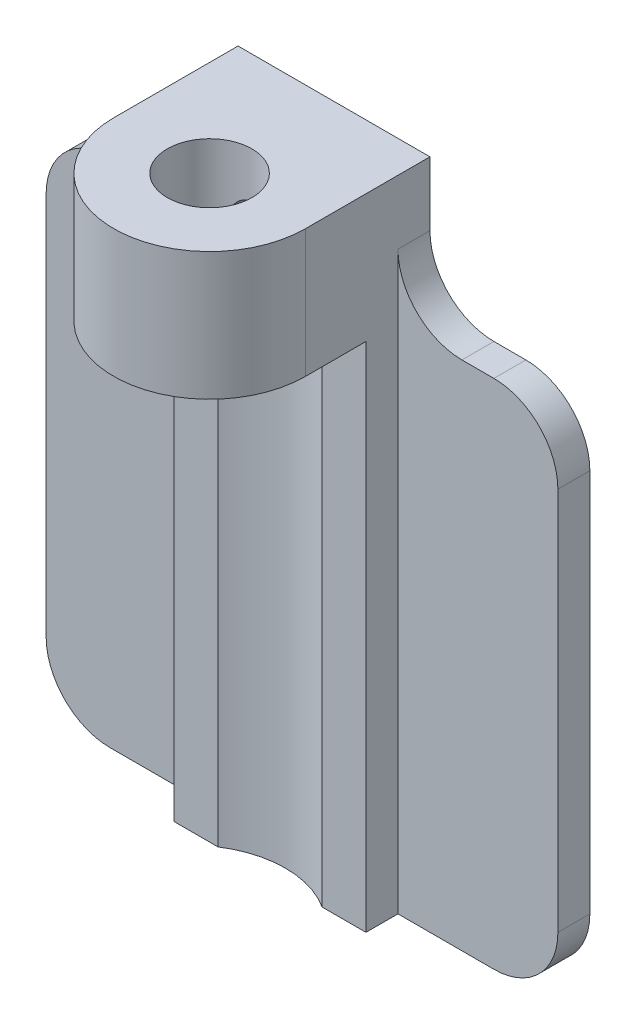
SolidWorks part; units mm, degrees
material "6061-T6 (SS)"
ref_plane "Front Plane" through (0, 0, 0) normal (0, 0, 1) x (1, 0, 0)
ref_plane "Top Plane" through (0, 0, 0) normal (0, 1, 0) x (1, 0, 0)
ref_plane "Right Plane" through (0, 0, 0) normal (1, 0, 0) x (0, 0, -1)
sketch "Sketch2" plane through (0, 0, 0) normal (1, 0, 0) x (0, 0, -1)
  line L0 (-4.7625, 12.7) -> (3, 12.7)
  line L1 (3, 12.7) -> (3, -12.7)
  line L2 (3, -12.7) -> (6.175, -12.7)
  line L3 (6.175, -12.7) -> (6.175, 19.05)
  line L4 (6.175, 19.05) -> (-4.7625, 19.05)
  line L5 (-4.7625, 19.05) -> (-4.7625, 12.7)
  line L6 (0, -1000) -> (0, 49000) construction
  dimension "D1" = 3
  dimension "D2" = 25.4
  dimension "D3" = 3.175
  dimension "D4" = 6.35
  dimension "D5" = 4.7625
  dimension "D6" = 12.7
extrude "Boss-Extrude1" add sketch "Sketch2" along normal mid plane 9.525
sketch "Sketch3" plane through (0, 19.05, 0) normal (0, 1, 0) x (1, 0, 0)
  circle A0 centre (0, 0) radius 2.1
  dimension "D1" = 4.2
extrude "Cut-Extrude1" cut sketch "Sketch3" against normal through all
sketch "Sketch4" plane through (0, -12.7, 0) normal (0, -1, 0) x (1, 0, 0)
  line L0 (4.7625, -3) -> (-4.7625, -3) construction
  circle A0 centre (0, 1.0005) radius 4.7625
  dimension "D1" = 9.525
  dimension "D2" = 0.762
extrude "Cut-Extrude2" cut sketch "Sketch4" against normal up to surface (25.4 mm away) up to face at (0, 12.7, 2.1)
ref_plane "Plane1" through (0, 0, -3.508) normal (0, 0, 1) x (1, 0, 0)
sketch "Sketch5" plane through (0, 0, -6.175) normal (0, 0, -1) x (-1, 0, 0)
  line L0 (2.5841, -12.7) -> (2.5841, 12.7) construction
  line L1 (-12.7, 12.7) -> (-2.5841, 12.7)
  line L2 (-12.7, 12.7) -> (-12.7, -12.7)
  line L3 (-12.7, -12.7) -> (-2.5841, -12.7)
  line L4 (12.7, 12.7) -> (12.7, -12.7)
  line L5 (-12.7, 12.7) -> (12.7, -12.7) construction
  line L6 (-12.7, -12.7) -> (12.7, 12.7) construction
  line L7 (-2.5841, 12.7) -> (-2.5841, -12.7) construction
  line L8 (2.5841, -12.7) -> (2.5841, 12.7)
  line L9 (-2.5841, 12.7) -> (-2.5841, -12.7)
  line L10 (2.5841, -12.7) -> (12.7, -12.7)
  line L11 (2.5841, 12.7) -> (12.7, 12.7)
  point P0 (0, 0)
  dimension "D1" = 25.4
extrude "Boss-Extrude2" add sketch "Sketch5" against normal blind 1.5875
sketch "Sketch6" plane through (0, 19.05, 0) normal (0, 1, 0) x (1, 0, 0)
  line L3 (4.7625, -4.7625) -> (-4.7625, -4.7625) construction
  circle A0 centre (0, 0) radius 4.7625
extrude "Cut-Extrude3" cut sketch "Sketch6" against normal blind 3.175 flip side to cut
sketch "Sketch7" plane through (0, 15.875, 0) normal (0, 1, 0) x (1, 0, 0)
  line L0 (-4.7625, 0) -> (-4.7625, -4.7625) construction
  line L1 (-4.7625, -4.7625) -> (0, -4.7625) construction
  line L2 (4.7625, 0) -> (4.7625, -4.7625) construction
  line L3 (0, -4.7625) -> (4.7625, -4.7625) construction
  line L4 (-4.7625, 0) -> (-4.7625, -4.7625)
  line L5 (-4.7625, -4.7625) -> (0, -4.7625)
  line L6 (4.7625, 0) -> (4.7625, -4.7625)
  line L7 (0, -4.7625) -> (4.7625, -4.7625)
  arc A0 (-4.7625, 0) -> (0, -4.7625) centre (0, 0) ccw construction
  arc A1 (0, -4.7625) -> (4.7625, 0) centre (0, 0) ccw construction
  arc A2 (-4.7625, 0) -> (0, -4.7625) centre (0, 0) ccw
  arc A3 (0, -4.7625) -> (4.7625, 0) centre (0, 0) ccw
extrude "Cut-Extrude4" cut sketch "Sketch7" against normal through all contours A2 L4 L5
sketch "Sketch8" plane through (0, 15.875, 0) normal (0, 1, 0) x (1, 0, 0)
  line L3 (4.7625, 6.175) -> (-4.7625, 6.175) construction
  line L5 (4.7625, 6.175) -> (4.7625, 0) construction
  line L6 (-4.7625, 6.175) -> (-4.7625, 0) construction
  line L7 (4.7625, 6.175) -> (4.7625, 0)
  line L8 (4.7625, 6.175) -> (-4.7625, 6.175)
  line L9 (-4.7625, 6.175) -> (-4.7625, 0)
  arc A0 (4.7625, 0) -> (-4.7625, 0) centre (0, 0) ccw construction
  arc A1 (4.7625, 0) -> (-4.7625, 0) centre (0, 0) ccw
extrude "Boss-Extrude3" add sketch "Sketch8" along normal up to surface (3.175 mm away) up to face at (0, 19.05, 2.1)
fillet "Fillet2" radius 3.175 6 edges at (-12.7, -12.7, -5.3813) (-12.7, 12.7, -5.3813) (-4.7625, 12.7, -5.3813) (12.7, -12.7, -5.3813) (12.7, 12.7, -5.3813) (4.7625, 12.7, -5.3813)
hole_wizard "#2-56 Tapped Hole1" positions "Sketch9" profile "Sketch10" tap size "#2-56" standard "ANSI Inch"
sketch "Sketch9" plane through (0, 0, -6.175) normal (0, 0, -1) x (-1, 0, 0)
  line L0 (4.7625, 19.05) -> (-4.7625, 19.05) construction
  point P0 (0, 15.875)
  dimension "D1" = 3.175
sketch "Sketch10" plane through (0, 15.875, -6.175) normal (1, 0, 0) x (0, 1, 0)
  line L0 (0, 0) -> (0, 4.075)
  line L1 (0, 4.075) -> (0.889, 4.075)
  line L2 (0.889, 4.075) -> (0.889, 0)
  line L5 (0.889, 0) -> (0, 0)
  line L11 (0, -6.35) -> (0, 107.95) construction
  dimension "Thru Tap Drill Dia." = 1.778
  dimension "Thru Tap Drill Depth" = 4.075
cosmetic thread "Hole Thread1" parameters "D2"=2.1844
